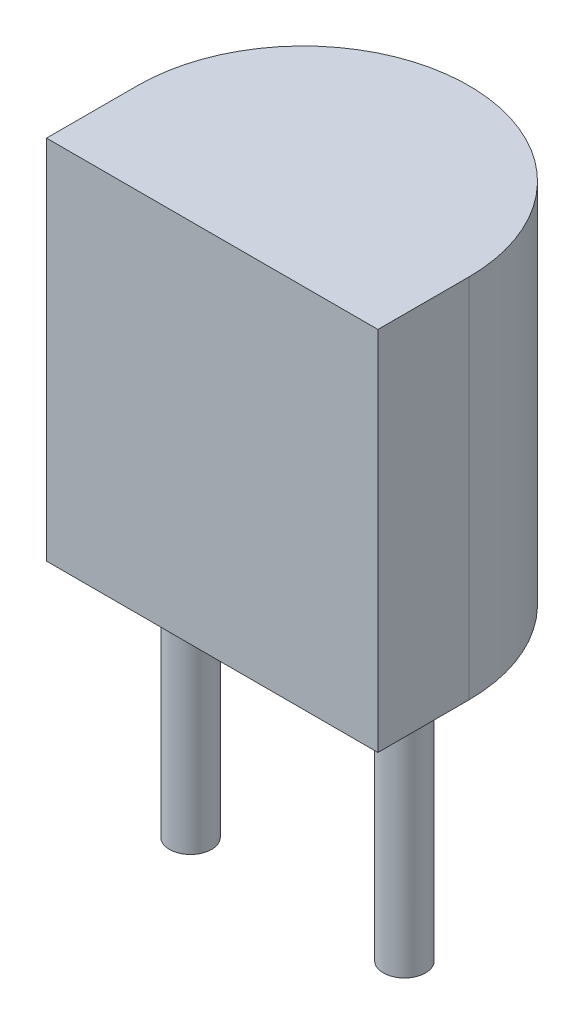
SolidWorks part; units mm, degrees
ref_plane "Front" through (0, 0, 0) normal (0, 0, 1) x (1, 0, 0)
ref_plane "Top" through (0, 0, 0) normal (0, 1, 0) x (1, 0, 0)
ref_plane "Right" through (0, 0, 0) normal (1, 0, 0) x (0, 0, -1)
ref_plane "Plane1" through (0, 3, 0) normal (0, 1, 0) x (-1, 0, 0)
sketch "Sketch 1" plane through (0, 3, 0) normal (0, 1, 0) x (0, 0, 1)
  line L1 (-0.13, 1.4) -> (2.03, 1.4)
  line L3 (-0.13, -6.47) -> (2.03, -6.47)
  line L4 (2.03, 1.4) -> (2.03, -6.47)
  arc A0 (-0.13, 1.4) -> (-0.13, -6.47) centre (-0.13, -2.535) ccw
  dimension "D4" = 2.16
  dimension "D1" = 7.87
  dimension "D2" = 1.4
  dimension "D3" = 2.03
extrude "Boss-Extrude 1" add sketch "Sketch 1" along normal blind 8.7
sketch "Sketch 2" plane through (0, 3, 0) normal (0, -1, 0) x (1, 0, 0)
  line L0 (0, 0) -> (-5.08, 0) construction
  line L1 (-2.54, 0) -> (-2.54, -2.54) construction
  line L2 (0, 0) -> (-2.54, -2.54) construction
  circle A0 centre (0, 0) radius 0.5
  circle A2 centre (-2.54, -2.54) radius 0.5
  circle A3 centre (-5.08, 0) radius 0.5
  dimension "D1" = 1
  dimension "D2" = 5.08
  dimension "D3" = 2.54
extrude "Boss-Extrude 2" add sketch "Sketch 2" along normal blind 6
ref_plane "Plane2" through (0, 0.5, 0) normal (0, 1, 0) x (-1, 0, 0)
sketch "Component_Outline" plane through (0, 0.5, 0) normal (0, 1, 0) x (-1, 0, 0)
  line L0 (-1.4, 2.03) -> (6.47, 2.03)
  line L1 (6.47, 2.03) -> (6.47, -0.13)
  line L2 (-1.4, -0.13) -> (-1.4, 2.03)
  arc A0 (6.47, -0.13) -> (-1.4, -0.13) centre (2.535, -0.13) cw
